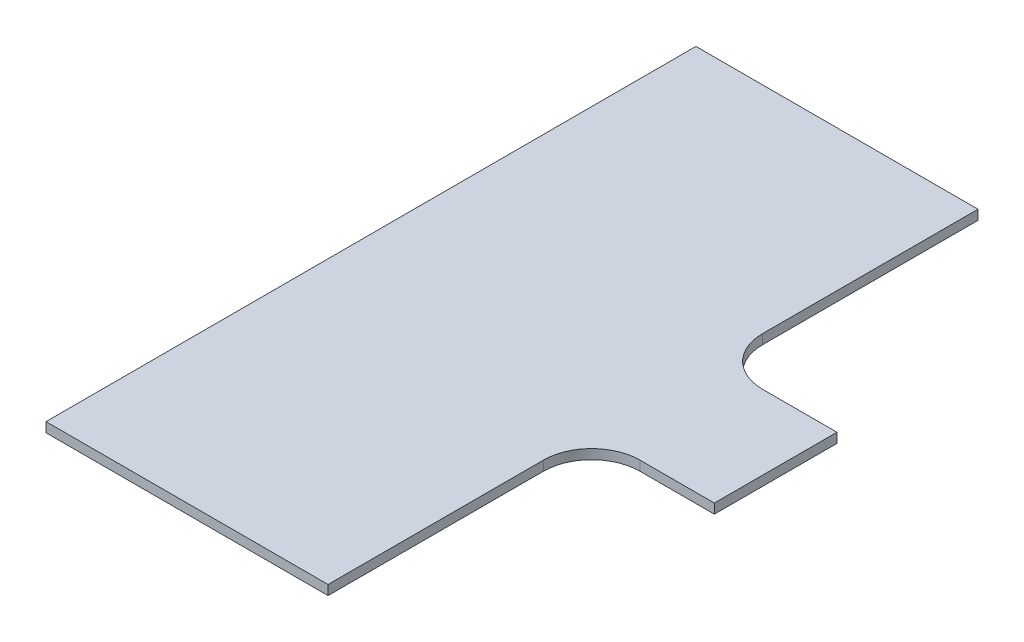
SolidWorks part; units mm, degrees
ref_plane "Front Plane" through (0, 0, 0) normal (0, 0, 1) x (1, 0, 0)
ref_plane "Top Plane" through (0, 0, 0) normal (0, 1, 0) x (1, 0, 0)
ref_plane "Right Plane" through (0, 0, 0) normal (1, 0, 0) x (0, 0, -1)
sketch "Sketch1" plane through (0, 0, 0) normal (0, 1, 0) x (1, 0, 0)
  line L0 (-29.21, 67.31) -> (29.21, -67.31) construction
  line L1 (-29.21, 67.31) -> (29.21, 67.31)
  line L2 (-29.21, 67.31) -> (-29.21, -67.31)
  line L3 (-29.21, -67.31) -> (29.21, -67.31)
  line L4 (29.21, 67.31) -> (29.21, 22.7)
  line L7 (29.21, -22.7) -> (29.21, -67.31)
  line L8 (39.21, 12.7) -> (54.61, 12.7)
  line L10 (39.21, -12.7) -> (54.61, -12.7)
  line L11 (54.61, 12.7) -> (54.61, -12.7)
  arc A0 (29.21, -22.7) -> (39.21, -12.7) centre (39.21, -22.7) cw
  arc A1 (39.21, 12.7) -> (29.21, 22.7) centre (39.21, 22.7) cw
  point P8 (29.21, -12.7)
  dimension "D5" = 10
  dimension "D1" = 58.42
  dimension "D2" = 134.62
  dimension "D3" = 25.4
  dimension "D4" = 25.4
extrude "Boss-Extrude1" add sketch "Sketch1" along normal blind 2
